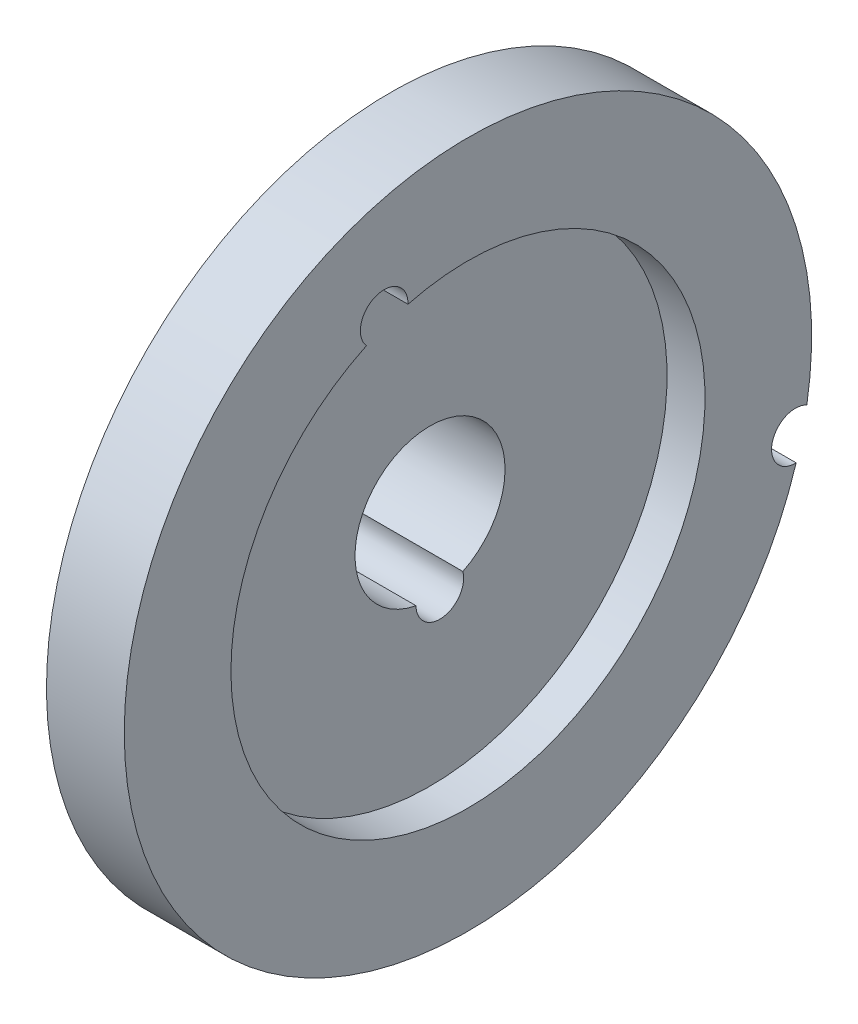
SolidWorks part; units mm, degrees
material "6061 Alloy"
ref_plane "Front Plane" through (0, 0, 0) normal (0, 0, 1) x (1, 0, 0)
ref_plane "Top Plane" through (0, 0, 0) normal (0, 1, 0) x (1, 0, 0)
ref_plane "Right Plane" through (0, 0, 0) normal (1, 0, 0) x (0, 0, -1)
sketch "Sketch1" plane through (0, 0, 0) normal (0, 0, 1) x (1, 0, 0)
  line L0 (0, 0) -> (-647.0721, 0) construction
  line L1 (-27.8573, 8.0391) -> (-14.0241, 8.0391)
  line L2 (-14.0241, 8.0391) -> (-14.0241, 25.4)
  line L3 (-14.0241, 25.4) -> (-9.9601, 25.4)
  line L5 (-18.2958, 17.8013) -> (-27.8573, 17.8013) construction
  line L6 (-27.8573, 17.8013) -> (-27.8573, 8.0391)
  line L7 (-9.9601, 25.4) -> (-9.9601, 36.83)
  line L8 (-9.9601, 36.83) -> (-18.2958, 36.83)
  line L10 (-12.8446, -23.9061) -> (-22.4061, -23.9061) construction
  line L11 (-4.5089, -34.3169) -> (-12.8446, -34.3169) construction
  line L12 (-18.2958, 36.83) -> (-27.8573, 17.8013)
  dimension "D1" = 16.0782
  dimension "D2" = 50.8
  dimension "D3" = 4.064
  dimension "D4" = 73.66
revolve "Revolve1" add sketch "Sketch1" angle 360 about L0
sketch "Sketch2" plane through (-9.9601, 0, 0) normal (1, 0, 0) x (0, 0, -1)
  circle A0 centre (46.0935, 23.8221) radius 2.032 construction
  circle A1 centre (18.8603, 44.2441) radius 2.032 construction
  circle A2 centre (-8.9778, 24.6544) radius 2.032 construction
  circle A3 centre (1.0507, -7.8746) radius 2.032 construction
  circle A4 centre (35.0866, -8.389) radius 2.032 construction
  circle A5 centre (46.0935, 23.8221) radius 2.032 construction
  circle A6 centre (18.8603, 44.2441) radius 2.032 construction
  circle A7 centre (-8.9778, 24.6544) radius 2.032 construction
  circle A8 centre (1.0507, -7.8746) radius 2.032 construction
  circle A9 centre (35.0866, -8.389) radius 2.032 construction
  circle A10 centre (35.0866, -8.389) radius 2.5527
  circle A11 centre (1.0507, -7.8746) radius 2.5527
  circle A12 centre (18.8603, 44.2441) radius 2.5527
  circle A13 centre (46.0935, 23.8221) radius 2.5527
  circle A14 centre (-8.9778, 24.6544) radius 2.5527
  dimension "D1" = 5.1054
extrude "Cut-Extrude1" cut sketch "Sketch2" against normal through all
